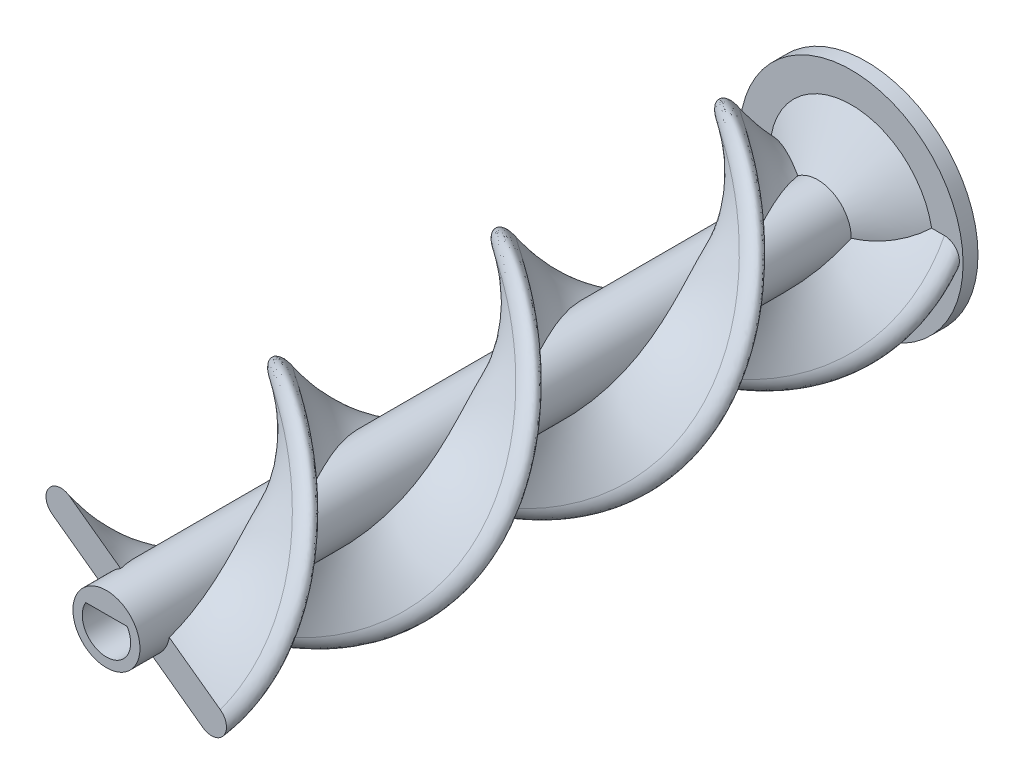
SolidWorks part; units mm, degrees
ref_plane "Front Plane" through (0, 0, 0) normal (0, 0, 1) x (1, 0, 0)
ref_plane "Top Plane" through (0, 0, 0) normal (0, 1, 0) x (1, 0, 0)
ref_plane "Right Plane" through (0, 0, 0) normal (1, 0, 0) x (0, 0, -1)
sketch "Sketch1" plane through (0, 0, 0) normal (0, 0, 1) x (1, 0, 0)
  circle A0 centre (0, 0) radius 4.5
  dimension "D1" = 9
extrude "Boss-Extrude1" add sketch "Sketch1" along normal blind 100
sketch "Sketch2" plane through (0, 0, 0) normal (0, 0, 1) x (1, 0, 0)
  line L0 (-12.5, 0) -> (12.5, 0) construction
  line L1 (-12.5, 2) -> (12.5, 2)
  line L2 (-12.5, -2) -> (12.5, -2)
  arc A0 (-12.5, 2) -> (-12.5, -2) centre (-12.5, 0) ccw
  arc A1 (12.5, -2) -> (12.5, 2) centre (12.5, 0) ccw
  point P2 (0, 0)
  dimension "D2" = 2
  dimension "D1" = 25
sketch "Sketch3" plane through (0, 0, 0) normal (0, 0, 1) x (1, 0, 0)
  circle A0 centre (0, 0) radius 14.5
  arc A1 (12.5, -2) -> (12.5, 2) centre (12.5, 0) ccw construction
curve "Helix/Spiral1" pitch 60 height 96 turns 1.6
sweep "Sweep1" add profiles "Sketch2" path "Helix/Spiral1"
sketch "Sketch5" plane through (0, 0, 0) normal (0, 0, -1) x (-1, 0, 0)
  circle A0 centre (0, 0) radius 15
  dimension "D1" = 30
extrude "Boss-Extrude2" add sketch "Sketch5" along normal blind 2
sketch "Sketch6" plane through (0, 0, 0) normal (0, 1, 0) x (1, 0, 0)
  line L0 (0, 0) -> (-10.9585, 0)
  line L1 (-4.0311, 0) -> (-12.5, 0) construction
  line L2 (-10.9585, 0) -> (0, -7.6692)
  line L3 (0, -7.6692) -> (0, 0)
revolve "Revolve1" add sketch "Sketch6" angle 360 about L3
sketch "Sketch4" plane through (0, 0, 100) normal (0, 0, 1) x (1, 0, 0)
  line L0 (-2.7699, 1.7) -> (2.7699, 1.7)
  arc A0 (-2.7699, 1.7) -> (2.7699, 1.7) centre (0, 0) ccw
  dimension "D1" = 6.5
  dimension "D2" = 1.7
extrude "Cut-Extrude1" cut sketch "Sketch4" against normal through all
